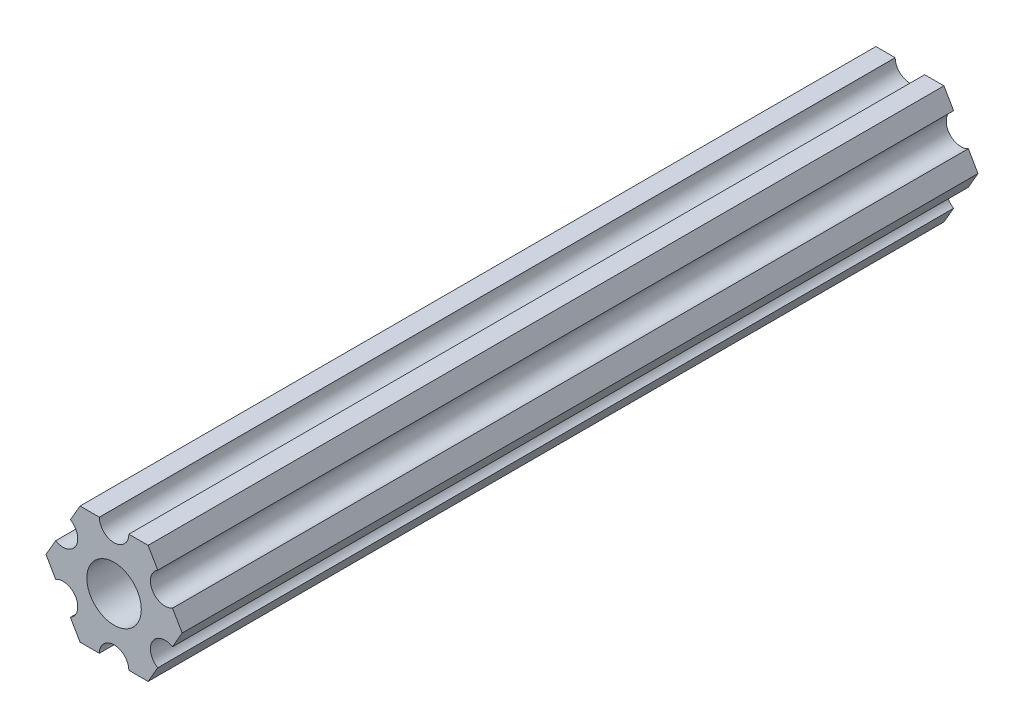
SolidWorks part; units mm, degrees
ref_plane "Front Plane" through (0, 0, 0) normal (0, 0, 1) x (1, 0, 0)
ref_plane "Top Plane" through (0, 0, 0) normal (0, 1, 0) x (1, 0, 0)
ref_plane "Right Plane" through (0, 0, 0) normal (1, 0, 0) x (0, 0, -1)
sketch "Sketch1" plane through (0, 0, 0) normal (0, 0, 1) x (1, 0, 0)
  line L0 (-1.5875, 6.35) -> (-3.6662, 6.35)
  line L1 (7.3323, 0) -> (6.293, 1.8002)
  line L2 (3.6662, 6.35) -> (1.5875, 6.35)
  line L3 (-3.6662, 6.35) -> (-4.7055, 4.5498)
  line L4 (-7.3323, 0) -> (-6.293, -1.8002)
  line L5 (-3.6662, -6.35) -> (-1.5875, -6.35)
  line L6 (3.6662, -6.35) -> (4.7055, -4.5498)
  line L7 (-6.293, 1.8002) -> (-7.3323, 0)
  line L8 (-4.7055, -4.5498) -> (-3.6662, -6.35)
  line L9 (1.5875, -6.35) -> (3.6662, -6.35)
  line L10 (6.293, -1.8002) -> (7.3323, 0)
  line L11 (4.7055, 4.5498) -> (3.6662, 6.35)
  circle A0 centre (0, 0) radius 2.9337
  arc A2 (-1.5875, 6.35) -> (1.5875, 6.35) centre (0, 6.35) ccw
  arc A3 (4.7055, 4.5498) -> (6.293, 1.8002) centre (5.4993, 3.175) ccw
  arc A4 (6.293, -1.8002) -> (4.7055, -4.5498) centre (5.4993, -3.175) ccw
  arc A5 (1.5875, -6.35) -> (-1.5875, -6.35) centre (0, -6.35) ccw
  arc A6 (-4.7055, -4.5498) -> (-6.293, -1.8002) centre (-5.4993, -3.175) ccw
  arc A7 (-6.293, 1.8002) -> (-4.7055, 4.5498) centre (-5.4993, 3.175) ccw
  dimension "D1" = 5.8674
  dimension "D3" = 3.175
  dimension "D4" = 6
extrude "Boss-Extrude1" add sketch "Sketch1" along normal blind 85.725
